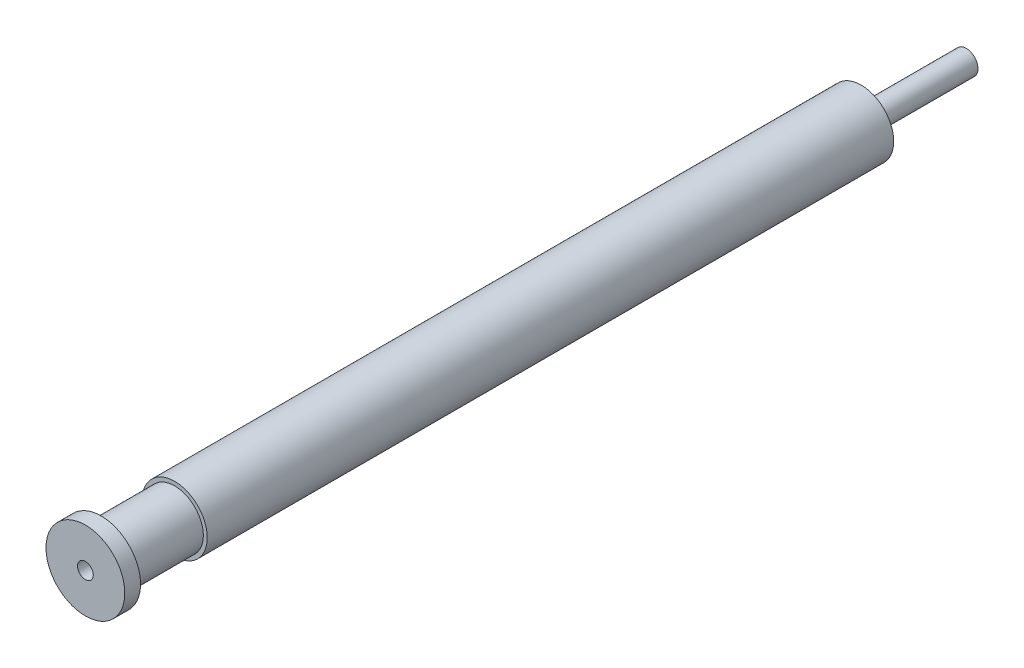
SolidWorks part; units mm, degrees
ref_plane "Front Plane" through (0, 0, 0) normal (0, 0, 1) x (1, 0, 0)
ref_plane "Top Plane" through (0, 0, 0) normal (0, 1, 0) x (1, 0, 0)
ref_plane "Right Plane" through (0, 0, 0) normal (1, 0, 0) x (0, 0, -1)
sketch "linear trace" plane through (0, 0, 0) normal (0, 1, 0) x (1, 0, 0)
  line L0 (160, 640) -> (800, 640) construction
  line L1 (24.8682, 43.7808) -> (24.8682, 17.0056)
  line L2 (24.8682, 17.0056) -> (24.8682, -55.9944)
  line L3 (25.1593, 43.7784) -> (27.244, 18.0728) construction
  line L4 (23.9729, 43.7784) -> (22.4925, 18.0728) construction
  line L5 (22.4925, 18.0728) -> (27.244, 18.0728) construction
  arc A0 (24.9673, 68.7253) -> (22.5853, 64.4044) centre (26.246, 65.2034) ccw
  arc A1 (22.5853, 64.4044) -> (24.8682, 43.7808) centre (-74.4553, 43.2243) cw
  point P13 (24.8682, 18.0728)
sketch "Sketch2" plane through (0, 0, 0) normal (0, 1, 0) x (1, 0, 0)
  line L0 (24.8682, 17.0056) -> (24.8682, -55.9944) construction
  line L1 (24.8682, 43.7808) -> (24.8682, 17.0056) construction
  line L2 (24.8682, 17.0056) -> (24.8682, -55.9944)
  line L3 (24.8682, 43.7808) -> (24.8682, 17.0056) construction
  line L4 (24.8682, 43.7808) -> (25.1344, 43.7808) construction
  line L5 (25.1344, 43.7808) -> (25.9932, 17.8476) construction
  line L6 (27.9682, 17.8476) -> (27.9682, -47.4944)
  line L7 (27.5932, -47.4944) -> (27.5932, -54.4944)
  line L8 (27.5932, -54.4944) -> (28.6182, -54.4944)
  line L9 (28.6182, -54.4944) -> (28.6182, -55.9944)
  line L10 (28.6182, -55.9944) -> (24.8682, -55.9944)
  line L11 (27.5932, -47.4944) -> (27.9682, -47.4944)
  line L12 (25.9932, 17.8476) -> (27.9682, 17.8476)
  line L13 (25.9932, 17.8476) -> (25.9932, 27.8476)
  line L14 (25.9932, 27.8476) -> (24.8682, 27.8476)
  line L15 (24.8682, 27.8476) -> (24.8682, 17.0056)
  dimension "D1" = 3.1
  dimension "D2" = 73
  dimension "D3" = 2.725
  dimension "D4" = 3.75
  dimension "D5" = 1.5
  dimension "D6" = 7
  dimension "D7" = 1.125
  dimension "D8" = 10
revolve "Revolve4" add sketch "Sketch2" angle 360 about L2
ref_plane "Plane1" [suppressed] through (0, 0, 55.9944) normal (0, 0, 1) x (1, 0, 0)
sketch "Sketch3" plane through (0, 0, 55.9944) normal (0, 0, 1) x (1, 0, 0)
  circle A0 centre (24.8682, 0) radius 0.75
  circle A1 centre (24.8682, 0) radius 3.75 construction
  circle A2 centre (24.8682, 0) radius 3.75 construction
  dimension "D1" = 1.5
extrude "Cut-Extrude6" cut sketch "Sketch3" against normal through all contours A0
